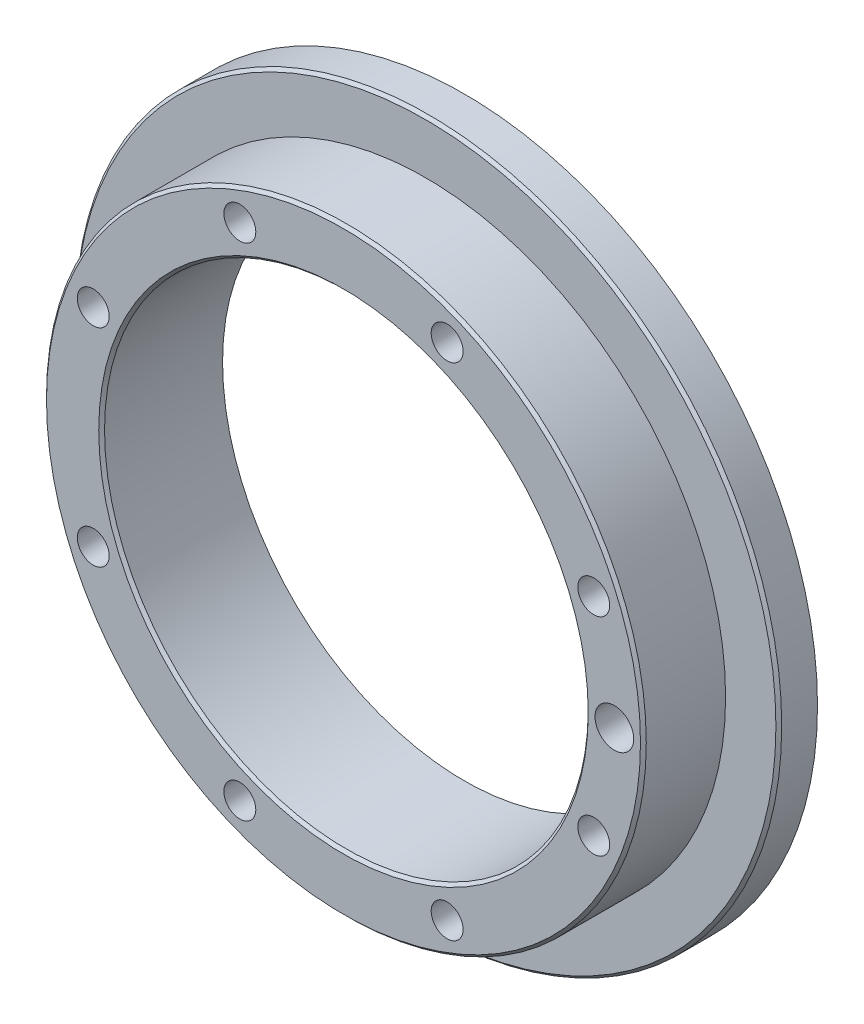
SolidWorks part; units mm, degrees
ref_plane "Front Plane" through (0, 0, 0) normal (0, 0, 1) x (1, 0, 0)
ref_plane "Top Plane" through (0, 0, 0) normal (0, 1, 0) x (1, 0, 0)
ref_plane "Right Plane" through (0, 0, 0) normal (1, 0, 0) x (0, 0, -1)
sketch "Sketch1" plane through (0, 0, 0) normal (0, 1, 0) x (1, 0, 0)
  line L0 (25, 0) -> (31, 0)
  line L1 (31, 0) -> (31, 8.5)
  line L2 (31, 8.5) -> (36.5, 8.5)
  line L3 (36.5, 8.5) -> (36.5, 12.5)
  line L4 (36.5, 12.5) -> (25, 12.5)
  line L5 (0, 0) -> (0, 12.5) construction
  line L6 (25, 12.5) -> (25, 0)
  line L7 (0, 0) -> (25, 0) construction
  line L8 (0, 12.5) -> (25, 12.5) construction
  dimension "D1" = 62
  dimension "D2" = 73
  dimension "D3" = 8.5
  dimension "D4" = 12.5
  dimension "D5" = 50
revolve "Revolve1" add sketch "Sketch1" angle 360 about L5
chamfer "Chamfer1" distance 0.3 angle 45 3 edges at (25, 0, 0) (31, 0, 0) (36.5, 0, -8.5)
sketch "Sketch4" plane through (0, 0, 0) normal (0, 0, 1) x (1, 0, 0)
  line L0 (0, 0) -> (0, -28) construction
  line L1 (0, 0) -> (28, 0) construction
  line L2 (0, 0) -> (25.8686, -10.7151) construction
  circle A0 centre (0, 0) radius 28 construction
  dimension "D1" = 56
  dimension "D2" = 22.5
hole_wizard "Ø4.000 x 6.0 Dowel" positions "Sketch3" profile "Sketch2" hole size "Ø4.0" standard "Ansi Metric"
sketch "Sketch3" plane through (0, 0, 0) normal (0, 0, 1) x (1, 0, 0)
  point P0 (28, 0)
sketch "Sketch2" plane through (28, 0, 0) normal (1, 0, 0) x (0, -1, 0)
  line L0 (0, 0) -> (0, 7.2017)
  line L1 (0, 7.2017) -> (2, 6)
  line L2 (2, 6) -> (2, 0)
  line L5 (2, 0) -> (0, 0)
  line L10 (0, 7.2017) -> (-2, 6) construction
  line L11 (0, -6.35) -> (0, 107.95) construction
  dimension "Hole Dia." = 4
  dimension "Hole Depth" = 6
  dimension "Drill Angle" = 118
hole_wizard "M4x0.7 x 6.0 Tapped Hole" positions "Sketch6" profile "Sketch5" tap size "M4x0.7" standard "Ansi Metric"
sketch "Sketch6" plane through (0, 0, 0) normal (0, 0, 1) x (1, 0, 0)
  point P0 (25.8686, -10.7151)
sketch "Sketch5" plane through (25.8686, -10.7151, 0) normal (1, 0, 0) x (0, -1, 0)
  line L0 (0, 0) -> (0, 12.4914)
  line L1 (0, 12.4914) -> (1.65, 11.5)
  line L2 (1.65, 11.5) -> (1.65, 0)
  line L5 (1.65, 0) -> (0, 0)
  line L10 (0, 12.4914) -> (-1.65, 11.5) construction
  line L11 (0, -6.35) -> (0, 107.95) construction
  dimension "Tap Drill Dia." = 3.3
  dimension "Tap Drill Depth" = 11.5
  dimension "Drill Angle" = 118
cosmetic thread "Hole Thread1" parameters "D1"=8, "D2"=4
pattern_circular "CirPattern1" count 8 over 360 about axis through (0, 0, 0) along (0, 0, 1) of "M4x0.7 x 6.0 Tapped Hole"
